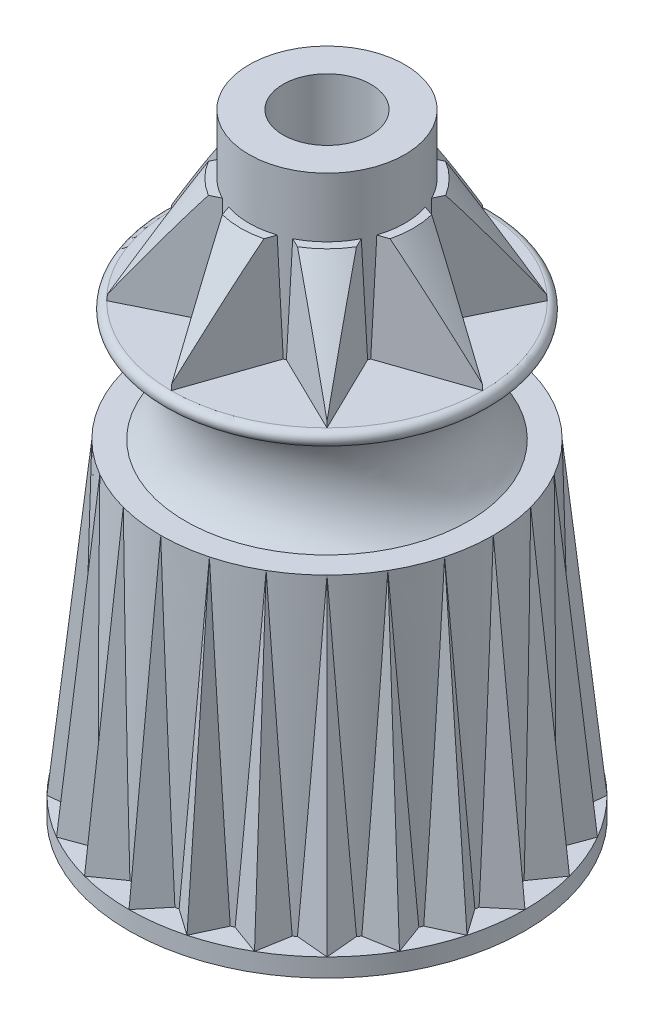
SolidWorks part; units mm, degrees
material "CA"
ref_plane "Front Plane" through (0, 0, 0) normal (0, 0, 1) x (1, 0, 0)
ref_plane "Top Plane" through (0, 0, 0) normal (0, 1, 0) x (1, 0, 0)
ref_plane "Right Plane" through (0, 0, 0) normal (1, 0, 0) x (0, 0, -1)
sketch "Sketch1" plane through (0, 0, 0) normal (0, 1, 0) x (1, 0, 0)
  circle A0 centre (0, 0) radius 8.89
  dimension "D1" = 17.78
extrude "Boss-Extrude1" add sketch "Sketch1" along normal blind 0.8128 draft 1
ref_plane "Plane1" through (0, 14.6304, 0) normal (0, 1, 0) x (1, 0, 0)
sketch "Sketch2" plane through (0, 14.6304, 0) normal (0, 1, 0) x (1, 0, 0)
  circle A0 centre (0, 0) radius 7.4549
  dimension "D1" = 14.9098
sketch "Sketch3" plane through (0, 0.8128, 0) normal (0, 1, 0) x (1, 0, 0)
  circle A0 centre (0, 0) radius 7.8105
  dimension "D1" = 15.621
loft "Loft1" add profiles "Sketch2", "Sketch3"
sketch "Sketch4" plane through (0, 0, 0) normal (1, 0, 0) x (0, 0, -1)
  line L0 (-7.4549, 14.6304) -> (-7.8105, 0.8128) construction
  line L1 (-7.4549, 14.6304) -> (-7.8105, 0.8128) construction
  line L2 (-8.8758, 0.8128) -> (-8.89, 0) construction
  line L3 (-8.8758, 0.8128) -> (-8.89, 0) construction
  line L4 (-8.8758, 0.8128) -> (-7.4549, 14.6304)
ref_plane "Plane2" through (0, 0.8128, 8.8758) normal (0, 0.9948, -0.1023) x (1, 0, 0)
sketch "Sketch5" plane through (0, 0.8128, 8.8758) normal (0, 0.9948, -0.1023) x (1, 0, 0)
  line L0 (0, 0) -> (0, 2.0328) construction
  line L1 (0, 0) -> (0, 1.0597) construction
  line L2 (0, 0) -> (1.2788, 1.524)
  line L3 (0, 0) -> (-1.2788, 1.524)
  line L4 (1.2788, 1.524) -> (-1.2788, 1.524)
  ellipse E0 centre (0, 8.8293) end of major axis (-8.8758, 8.8293) minor radius 8.8293 construction
  dimension "D1" = 80
  dimension "D2" = 1.524
sweep "Sweep1" add profiles "Sketch5" path "Sketch4"
pattern_circular "CirPattern1" count 24 over 360 about axis through (0, 0, 0) along (0, 1, 0) of "Sweep1"
sketch "Sketch7" plane through (0, 0, 0) normal (1, 0, 0) x (0, 0, -1)
  line L0 (0, 0) -> (0, 25.5262) construction
  line L1 (0, 0.8128) -> (0, 14.6304) construction
  line L2 (0, 20.0152) -> (6.985, 20.0152)
  line L3 (6.985, 19.3802) -> (6.35, 19.3802)
  line L4 (1.9295, 14.6304) -> (0, 14.6304) construction
  line L6 (16.7407, 14.6304) -> (0, 14.6304) construction
  line L7 (6.35, 14.6304) -> (0, 14.6304)
  line L8 (0, 14.6304) -> (0, 20.0152)
  arc A0 (6.985, 20.0152) -> (6.985, 19.3802) centre (6.985, 19.6977) cw
  arc A1 (6.35, 19.3802) -> (6.35, 14.6304) centre (8.6591, 17.0053) ccw
  dimension "D4" = 10.6934
  dimension "D1" = 12.7
  dimension "D2" = 0.635
  dimension "D3" = 0.635
  dimension "D5" = 4.7498
revolve "Revolve1" add sketch "Sketch7" angle 360 about L8
sketch "Sketch8" plane through (0, 20.0152, 0) normal (0, 1, 0) x (1, 0, 0)
  circle A0 centre (0, 0) radius 3.4925
  dimension "D1" = 6.985
extrude "Boss-Extrude2" add sketch "Sketch8" along a picked direction on the side of the normal offset from surface (7.4168 mm away) 27.432
sketch "Sketch9" plane through (0, 27.432, 0) normal (0, 1, 0) x (1, 0, 0)
  circle A0 centre (0, 0) radius 1.9685
  dimension "D1" = 3.937
extrude "Cut-Extrude1" cut sketch "Sketch9" against normal through all
sketch "Sketch10" plane through (0, 20.0152, 0) normal (0, 1, 0) x (1, 0, 0)
  line L0 (0, 0) -> (0, -9.673) construction
  line L1 (0, -6.985) -> (-1.5664, -2.436)
  line L2 (0, -6.985) -> (1.5664, -2.436)
  line L3 (-1.5664, -2.436) -> (1.5664, -2.436)
  circle A0 centre (0, 0) radius 6.985 construction
  dimension "D1" = 4.549
  dimension "D2" = 38
extrude "Boss-Extrude3" add sketch "Sketch10" along normal offset from surface 2.667 draft 2
pattern_circular "CirPattern2" count 8 over 360 about axis through (0, 0, 0) along (0, 1, 0) of "Boss-Extrude3"
sketch "Sketch11" plane through (0, 0, 0) normal (1, 0, 0) x (0, 0, -1)
  line L0 (3.4925, 24.765) -> (3.4925, 27.432) construction
  line L1 (3.4925, 24.765) -> (3.4925, 27.432)
  line L2 (6.4755, 24.765) -> (6.985, 20.0152) construction
  line L3 (6.4755, 24.765) -> (6.985, 20.0152) construction
  line L4 (3.4925, 24.765) -> (6.9579, 20.2678) construction
  line L5 (6.9579, 20.2678) -> (7.4659, 20.2678)
  line L6 (7.4659, 20.2678) -> (7.4659, 27.432)
  line L7 (7.4659, 27.432) -> (3.4925, 27.432)
  line L8 (3.4925, 24.765) -> (3.8735, 24.765)
  line L9 (1.5784, 24.765) -> (4.5789, 24.765) construction
  line L10 (3.8735, 24.765) -> (6.9579, 20.2678)
  dimension "D1" = 0.254
  dimension "D2" = 0.508
  dimension "D3" = 0.381
revolve "Cut-Revolve1" cut sketch "Sketch11" angle 360 about axis through (0, 64.7423, 0) along (0, -1, 0)
sketch "Sketch12" plane through (0, 0, 0) normal (1, 0, 0) x (0, 0, -1)
  line L0 (0, 0) -> (0, 28.1928) construction
  line L1 (2.921, 0) -> (3.1941, 15.6464)
  line L2 (3.1941, 15.6464) -> (4.5495, 15.6464)
  line L4 (-8.89, 0) -> (8.89, 0) construction
  line L5 (6.2319, 14.2909) -> (6.6263, 2.9972) construction
  line L6 (2.921, 0) -> (2.921, -2.54)
  line L7 (2.921, -2.54) -> (6.731, -2.54)
  line L8 (6.731, 0) -> (6.731, -2.54)
  line L9 (6.4484, 2.9972) -> (6.491, 1.778)
  line L10 (5.8897, 13.902) -> (6.2705, 2.9972)
  line L11 (6.491, 1.778) -> (6.6689, 1.778)
  line L12 (6.2705, 2.9972) -> (6.4484, 2.9972)
  line L13 (6.6689, 1.778) -> (6.731, 0)
  line L14 (6.0543, 14.2847) -> (6.5533, -0.0062) construction
  line L15 (5.8766, 14.2785) -> (6.3756, -0.0124) construction
  line L16 (5.6417, 13.902) -> (5.8897, 13.902)
  line L17 (6.2319, 14.2909) -> (6.731, 0) construction
  circle A0 centre (0, 0) radius 2.921 construction
  arc A1 (6.35, 19.3802) -> (6.35, 14.6304) centre (8.6591, 17.0053) ccw construction
  arc A2 (6.35, 19.3802) -> (6.35, 14.6304) centre (8.6591, 17.0053) ccw construction
  arc A3 (4.5495, 15.6464) -> (5.6417, 13.902) centre (8.6591, 17.0053) ccw
  circle A4 centre (0, 0) radius 6.731 construction
  arc A5 (5.6417, 20.1086) -> (5.6417, 13.902) centre (8.6591, 17.0053) ccw construction
  dimension "D1" = 5.842
  dimension "D6" = 13.462
  dimension "D3" = 1
  dimension "D4" = 15.6464
  dimension "D5" = 2
  dimension "D7" = 2.54
  dimension "D10" = 1.778
  dimension "D11" = 2.9972
  dimension "D2" = 1.016
  dimension "D8" = 0.1778
  dimension "D9" = 0.1778
revolve "Cut-Revolve2" cut sketch "Sketch12" angle 360 about L0
fillet "Fillet1" radius 0.762 1 edges at (0, 0, -6.731)
sketch "Sketch13" plane through (0, 1.778, 0) normal (0, -1, 0) x (1, 0, 0)
  line L0 (0, -6.491) -> (0, -2.4467)
  line L1 (0, 2.4467) -> (0, 6.491)
  circle A0 centre (0, 0) radius 6.491 construction
  circle A1 centre (0, 0) radius 2.4467 construction
rib "Rib1" sketch "Sketch13" sketch "Sketch13" thickness 1.016 parameters "D1"=1.016, "D3"=1
fillet "Fillet2" radius 0.508 8 edges at (0.508, 1.778, 4.6895) (-0.6093, 7.5791, 2.9919) (-0.508, 1.778, 4.6895) (0.6093, 7.5791, 2.9919) (-0.508, 1.778, -4.6895) (0.508, 1.778, -4.6895)
ref_plane "Plane3" through (0, 17.145, 0) normal (0, 1, 0) x (1, 0, 0)
sketch "Sketch14" plane through (0, 17.145, 0) normal (0, 1, 0) x (1, 0, 0)
  circle A0 centre (0, 0) radius 7.9375 construction
  dimension "D1" = 15.875
